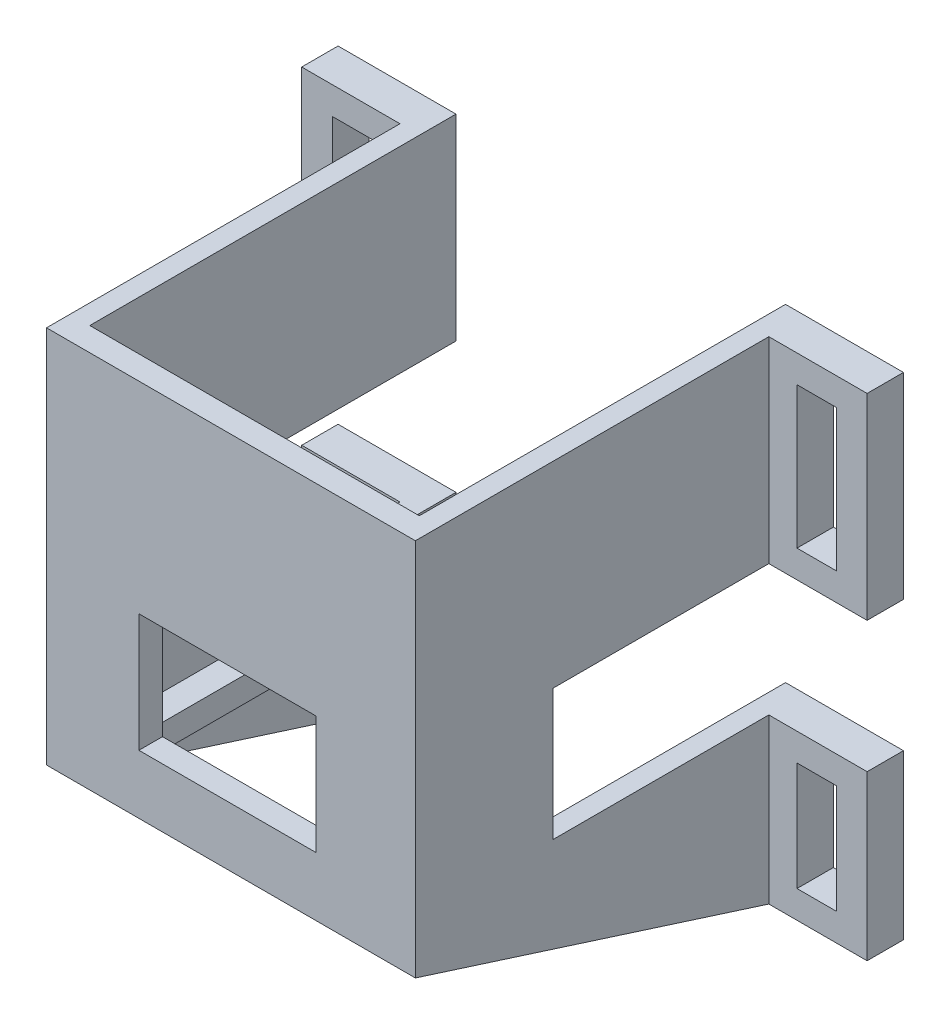
SolidWorks part; units mm, degrees
ref_plane "Front Plane" through (0, 0, 0) normal (0, 0, 1) x (1, 0, 0)
ref_plane "Top Plane" through (0, 0, 0) normal (0, 1, 0) x (1, 0, 0)
ref_plane "Right Plane" through (0, 0, 0) normal (1, 0, 0) x (0, 0, -1)
sketch "Sketch1" plane through (0, 0, 0) normal (0, 0, 1) x (1, 0, 0)
  line L0 (-180.1477, 0) -> (197.4813, 0) construction
  line L2 (0, -85.5209) -> (0, 332.6755) construction
  line L3 (0, 0) -> (0, 25)
  line L4 (0, 25) -> (15, 25)
  line L5 (15, 25) -> (15, 0)
  line L6 (15, 0) -> (0, 0)
  line L7 (15, 25) -> (15, 75)
  line L8 (15, 75) -> (71.3, 75)
  line L9 (71.3, 75) -> (71.3, 0)
  line L10 (71.3, 0) -> (15, 0)
  line L11 (15, 75) -> (0, 75)
  line L12 (0, 75) -> (0, 45)
  line L13 (0, 45) -> (15, 45)
  line L14 (71.3, 75) -> (98.5824, 75)
  line L15 (71.3, 0) -> (86.3, 0)
  line L16 (86.3, 0) -> (86.3, 25)
  line L17 (86.3, 25) -> (71.3, 25)
  line L18 (71.3, 75) -> (86.3, 75)
  line L19 (86.3, 75) -> (86.3, 45)
  line L20 (86.3, 45) -> (71.3, 45)
  line L22 (29.1, 44.25) -> (56.1, 44.25)
  line L23 (29.1, 44.25) -> (29.1, 26.2)
  line L24 (29.1, 26.2) -> (56.1, 26.2)
  line L25 (56.1, 44.25) -> (56.1, 26.2)
  dimension "D1" = 56.3
  dimension "D3" = 15
  dimension "D2" = 75
  dimension "D4" = 50
  dimension "D5" = 30
  dimension "D6" = 50
  dimension "D7" = 15
  dimension "D8" = 30
  dimension "D9" = 30.75
  dimension "D10" = 15.2
  dimension "D11" = 14.1
  dimension "D12" = 48.8
extrude "Boss-Extrude1" add sketch "Sketch1" along normal blind 59.5 contours L10 L9 L8 L7 L5 L22 L25 L24 L23 | L20 L19 L14 L9 | L16 L17 L9 L15 | L6 L5 L4 L3 | L12 L13 L7 L11
sketch "Sketch3" plane through (0, 0, 59.5) normal (0, 0, 1) x (1, 0, 0)
  line L0 (86.3, 0) -> (0, 0) construction
  line L1 (0, 75) -> (15, 75)
  line L2 (0, 75) -> (0, 0)
  line L3 (0, 0) -> (15, 0)
  line L4 (15, 75) -> (15, 0)
  line L6 (86.3, 75) -> (71.3, 75)
  line L7 (86.3, 75) -> (86.3, 0)
  line L8 (86.3, 0) -> (71.3, 0)
  line L9 (71.3, 75) -> (71.3, 0)
  dimension "D1" = 15
  dimension "D2" = 15
extrude "Cut-Extrude2" cut sketch "Sketch3" against normal blind 53.95
sketch "Sketch4" plane through (0, 0, 5.55) normal (0, 0, 1) x (1, 0, 0)
  line L0 (15, 0) -> (15, 25) construction
  line L1 (4.7, 20.8) -> (10.7, 20.8)
  line L2 (4.7, 20.8) -> (4.7, 4.2)
  line L3 (4.7, 4.2) -> (10.7, 4.2)
  line L4 (10.7, 20.8) -> (10.7, 4.2)
  line L5 (4.7, 70.8) -> (10.7, 70.8)
  line L6 (4.7, 70.8) -> (4.7, 49.2)
  line L7 (4.7, 49.2) -> (10.7, 49.2)
  line L8 (10.7, 70.8) -> (10.7, 49.2)
  line L9 (75.6, 70.8) -> (81.6, 70.8)
  line L10 (75.6, 70.8) -> (75.6, 49.2)
  line L11 (75.6, 49.2) -> (81.6, 49.2)
  line L12 (81.6, 70.8) -> (81.6, 49.2)
  line L13 (75.6, 20.8) -> (81.6, 20.8)
  line L14 (75.6, 20.8) -> (75.6, 4.2)
  line L15 (75.6, 4.2) -> (81.6, 4.2)
  line L16 (81.6, 20.8) -> (81.6, 4.2)
  line L17 (0, 0) -> (15, 0) construction
  line L18 (0, 25) -> (15, 25) construction
  line L20 (0, 45) -> (15, 45) construction
  line L21 (15, 75) -> (0, 75) construction
  line L22 (15, 0) -> (15, 75) construction
  line L23 (71.3, 75) -> (71.3, 0) construction
  line L24 (71.3, 0) -> (86.3, 0) construction
  line L25 (71.3, 25) -> (86.3, 25) construction
  line L26 (71.3, 45) -> (86.3, 45) construction
  line L27 (86.3, 75) -> (71.3, 75) construction
  dimension "D1" = 4.3
  dimension "D2" = 6
  dimension "D3" = 4.2
  dimension "D4" = 4.2
  dimension "D5" = 4.2
  dimension "D6" = 4.2
  dimension "D7" = 4.3
  dimension "D8" = 6
  dimension "D9" = 4.3
  dimension "D10" = 6
  dimension "D11" = 4.2
  dimension "D12" = 4.2
  dimension "D13" = 6
  dimension "D14" = 4.3
  dimension "D15" = 4.2
  dimension "D16" = 4.2
extrude "Cut-Extrude3" cut sketch "Sketch4" against normal blind 10
sketch "Sketch6" plane through (0, 75, 0) normal (0, 1, 0) x (1, 0, 0)
  line L0 (18, 0) -> (18, -55.9)
  line L1 (0, 0) -> (86.3, 0) construction
  line L2 (18, -55.9) -> (68.3, -55.9)
  line L3 (68.3, -55.9) -> (68.3, 0)
  line L4 (15, -59.5) -> (71.3, -59.5) construction
  line L5 (15, -5.55) -> (15, -59.5) construction
  line L6 (71.3, -5.55) -> (71.3, -59.5) construction
  dimension "D1" = 3.6
  dimension "D2" = 3
  dimension "D3" = 3
extrude "Cut-Extrude4" cut sketch "Sketch6" against normal blind 54 and the other way through all
sketch "Sketch7" plane through (0, 0, 0) normal (0, -1, 0) x (1, 0, 0)
  line L0 (18, 0) -> (18, 55.9)
  line L1 (86.3, 0) -> (0, 0) construction
  line L2 (18, 55.9) -> (68.3, 55.9)
  line L3 (68.3, 55.9) -> (68.3, 0)
  line L4 (15, 5.55) -> (15, 59.5) construction
  line L5 (71.3, 5.55) -> (71.3, 59.5) construction
  line L6 (71.3, 59.5) -> (15, 59.5) construction
  dimension "D1" = 3
  dimension "D2" = 3
  dimension "D3" = 3.6
extrude "Cut-Extrude5" cut sketch "Sketch7" against normal blind 17.2 and the other way through all flip side to cut
sketch "Sketch8" plane through (0, 0, 0) normal (0, 0, -1) x (-1, 0, 0)
  line L0 (-64.3, 21) -> (-64.3, 17.2)
  line L1 (-18, 21) -> (-68.3, 21) construction
  line L2 (-68.3, 17.2) -> (-18, 17.2) construction
  line L3 (-64.3, 17.2) -> (-22, 17.2)
  line L4 (-18, 17.2) -> (-68.3, 17.2) construction
  line L5 (-22, 17.2) -> (-22, 21)
  line L6 (-18, 21) -> (-68.3, 21) construction
  line L7 (-22, 21) -> (-64.3, 21)
  line L8 (-68.3, 0) -> (-68.3, 17.2) construction
  line L9 (-18, 0) -> (-18, 17.2) construction
  dimension "D1" = 4
  dimension "D2" = 4
extrude "Cut-Extrude6" cut sketch "Sketch8" against normal blind 51.9
sketch "Sketch9" plane through (15, 0, 0) normal (-1, 0, 0) x (0, 0, 1)
  line L0 (0, 45) -> (38.5, 45)
  line L1 (38.5, 45) -> (38.5, 25)
  line L2 (38.5, 25) -> (0, 25)
  dimension "D1" = 38.5
extrude "Cut-Extrude7" cut sketch "Sketch9" against normal blind 60 and the other way through all flip side to cut
sketch "Sketch11" plane through (71.3, 0, 0) normal (1, 0, 0) x (0, 0, -1)
  line L0 (-5.55, 0) -> (-59.5, 17.2)
  line L1 (-59.5, 75) -> (-59.5, 0) construction
  line L2 (-59.5, 17.2) -> (-59.5, 0)
  line L3 (-59.5, 0) -> (-5.55, 0)
  dimension "D1" = 17.2
extrude "Cut-Extrude8" cut sketch "Sketch11" against normal blind 60 contours L3 L0 L2
